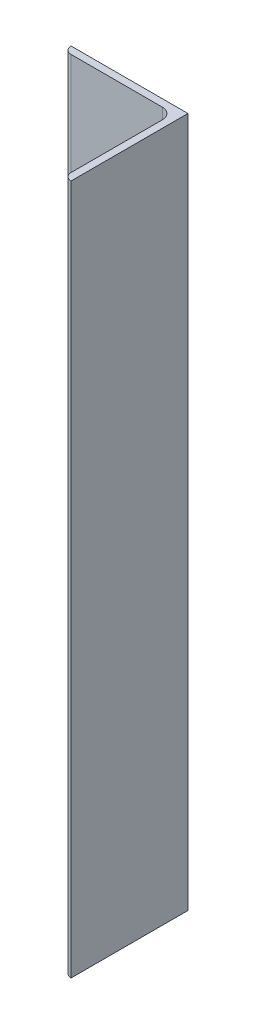
SolidWorks part; units mm, degrees
material "AISI 1020"
ref_plane "Alzado" through (0, 0, 0) normal (0, 0, 1) x (1, 0, 0)
ref_plane "Planta" through (0, 0, 0) normal (0, 1, 0) x (1, 0, 0)
ref_plane "Vista lateral" through (0, 0, 0) normal (1, 0, 0) x (0, 0, -1)
sketch "Croquis1" plane through (0, 0, 0) normal (0, 0, 1) x (1, 0, 0)
  line L0 (0, -150) -> (0, 150)
  point P4 (0, 0)
  dimension "D1" = 300
other "Hierro angular 2 X 2 X 0.125(1)"
ref_plane "Plano1" through (0, -150, 0) normal (0, 1, 0) x (-1, 0, 0)
sketch "Sketch11" plane through (0, -150, 0) normal (0, 1, 0) x (-1, 0, 0)
  line L0 (0, 0) -> (0, 50.8)
  line L1 (0, 50.8) -> (0.0051, 50.8)
  line L2 (3.175, 47.6301) -> (3.175, 7.9375)
  line L3 (7.9375, 3.175) -> (47.6301, 3.175)
  line L4 (50.8, 0.0051) -> (50.8, 0)
  line L5 (50.8, 0) -> (0, 0)
  arc A0 (50.8, 0.0051) -> (47.6301, 3.175) centre (47.6301, 0.0051) ccw
  arc A1 (0.0051, 50.8) -> (3.175, 47.6301) centre (0.0051, 47.6301) cw
  arc A2 (7.9375, 3.175) -> (3.175, 7.9375) centre (7.9375, 7.9375) cw
  point P10 (25.4, 0)
  point P14 (0, 25.4)
  point P15 (3.175, 25.4)
  point P16 (25.4, 3.175)
  point P17 (3.175, 50.8)
  point P18 (50.8, 3.175)
  point P19 (0, 0)
  dimension "D2" = 0.0051
  dimension "Radius_1" = 4.7625
  dimension "D1" = 3.175
  dimension "H_leg" = 50.8
